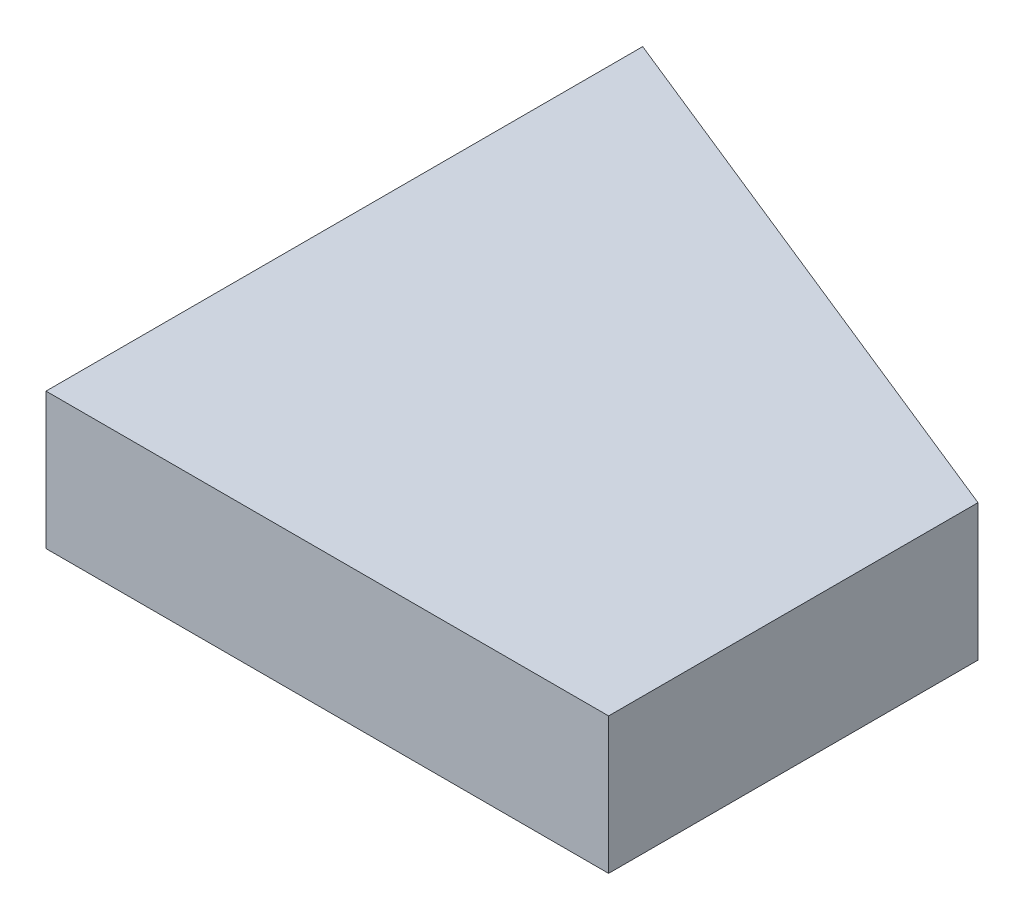
SolidWorks part; units mm, degrees
ref_plane "Front Plane" through (0, 0, 0) normal (0, 0, 1) x (1, 0, 0)
ref_plane "Top Plane" through (0, 0, 0) normal (0, 1, 0) x (1, 0, 0)
ref_plane "Right Plane" through (0, 0, 0) normal (1, 0, 0) x (0, 0, -1)
sketch "Sketch1" plane through (0, 0, 0) normal (0, 1, 0) x (1, 0, 0)
  line L0 (0, 0) -> (0, 28.885) construction
  line L1 (0, 0) -> (46.3009, 0) construction
  line L2 (0, 0) -> (33, 0)
  line L3 (0, 0) -> (0, 35)
  line L4 (33, 0) -> (33, 21.6671)
  line L5 (0, 35) -> (33, 21.6671)
  dimension "D1" = 35
  dimension "D2" = 33
  dimension "D3" = 68
extrude "Boss-Extrude2" add sketch "Sketch1" along normal blind 8
sketch "Sketch2" plane through (0, 0, 0) normal (1, 0, 0) x (0, 0, -1)
  line L0 (35, 4) -> (0, 4) construction
  line L1 (35, 8) -> (35, 0) construction
  line L2 (0, 8) -> (0, 0) construction
  line L3 (17.5, 8) -> (17.5, 0) construction
  line L4 (35, 8) -> (0, 8) construction
  line L5 (35, 0) -> (0, 0) construction
  circle A0 centre (17.5, 4) radius 1.5
  dimension "D1" = 3
extrude "Cut-Extrude1" cut sketch "Sketch2" along normal blind 20 from surface at 0 starting at face at (0, 4, -17.5)
